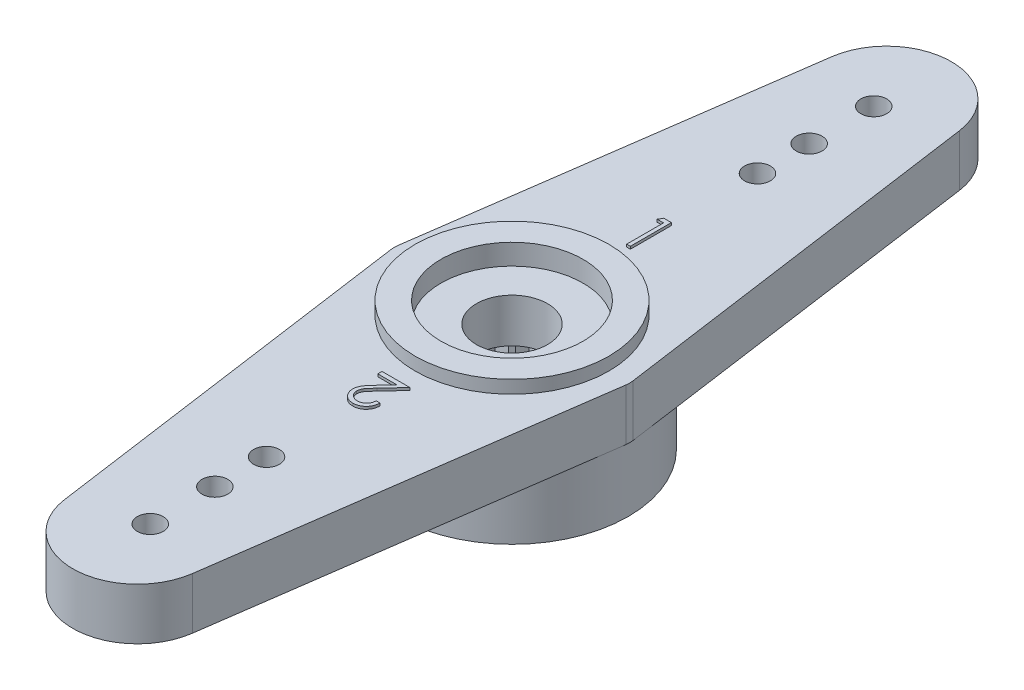
SolidWorks part; units mm, degrees
ref_plane "Front Plane" through (0, 0, 0) normal (0, 0, 1) x (1, 0, 0)
ref_plane "Top Plane" through (0, 0, 0) normal (0, 1, 0) x (1, 0, 0)
ref_plane "Right Plane" through (0, 0, 0) normal (1, 0, 0) x (0, 0, -1)
sketch "Sketch1" plane through (0, 0, 0) normal (0, 1, 0) x (1, 0, 0)
  line L0 (0, 17) -> (0, -17) construction
  line L1 (-17, 0) -> (17, 0) construction
  line L2 (-2.6883, 13.3345) -> (-4.0139, 3.9009) construction
  line L3 (4, -4) -> (-4, -4) construction
  line L4 (4, -4) -> (4, 4) construction
  line L5 (4, 4) -> (-4, 4) construction
  line L6 (-4, -4) -> (-4, 4) construction
  line L7 (4, -4) -> (-4, 4) construction
  line L8 (4, 4) -> (-4, -4) construction
  line L9 (-4, 4) -> (-2.4757, 14.8479)
  line L10 (4, 4) -> (2.4757, 14.8479)
  line L11 (4, -4) -> (2.4757, -14.8479)
  line L12 (-4, -4) -> (-2.4757, -14.8479)
  line L13 (-4, 4) -> (-4.5621, 0)
  line L14 (4, 4) -> (4.5621, 0)
  line L15 (4, -4) -> (4.5621, 0)
  line L16 (-4, -4) -> (-4.5621, 0)
  circle A0 centre (0, 0) radius 17 construction
  circle A1 centre (0, 0) radius 16 construction
  arc A2 (2.4757, 14.8479) -> (-2.4757, 14.8479) centre (0, 14.5) ccw
  arc A3 (2.4757, -14.8479) -> (-2.4757, -14.8479) centre (0, -14.5) cw
  circle A6 centre (0, 0) radius 14 construction
  circle A7 centre (0, 0) radius 11.5 construction
  circle A8 centre (0, 0) radius 9.5 construction
  circle A9 centre (0, 14) radius 0.5
  circle A10 centre (0, 11.5) radius 0.5
  circle A11 centre (0, 9.5) radius 0.5
  circle A12 centre (0, -14) radius 0.5
  circle A13 centre (0, -11.5) radius 0.5
  circle A14 centre (0, -9.5) radius 0.5
  circle A21 centre (0, 0) radius 1.375
  point P13 (-4.5621, 0)
  point P59 (0, 0)
  dimension "D1" = 34
  dimension "D2" = 1
  dimension "D3" = 5
  dimension "D5" = 8
  dimension "D6" = 8
  dimension "D7" = 2.5
  dimension "D9" = 28
  dimension "D11" = 1
  dimension "D12" = 1
  dimension "D13" = 2
  dimension "D8" = 4.5
  dimension "D10" = 1
  dimension "D14" = 2.75
extrude "Boss-Extrude1" add sketch "Sketch1" along normal blind 2
sketch "Sketch2" plane through (0, 2, 0) normal (0, 1, 0) x (1, 0, 0)
  circle A0 centre (0, 0) radius 3.75
  circle A1 centre (0, 0) radius 2.75
  dimension "D1" = 7.5
  dimension "D2" = 1
extrude "Boss-Extrude2" add sketch "Sketch2" along normal blind 0.5
sketch "Sketch3" plane through (0, 2.5, 0) normal (0, 1, 0) x (1, 0, 0)
  circle A2 centre (0, 0) radius 1.375
  circle A3 centre (0, 0) radius 2.75
  circle A5 centre (0, 0) radius 2.75
  circle A6 centre (0, 0) radius 2.75
  circle M6 centre (0, 0) radius 2.75
  dimension "D1" = 0
extrude "Cut-Extrude1" cut sketch "Sketch3" against normal blind 0.8 contours A2 M6
sketch "Sketch4" plane through (0, 0, 0) normal (0, -1, 0) x (1, 0, 0)
  circle A0 centre (0, 0) radius 4.5
  circle A1 centre (0, 0) radius 2.5
  dimension "D1" = 9
  dimension "D2" = 2
extrude "Boss-Extrude3" add sketch "Sketch4" along normal blind 2.5
sketch "Sketch5" plane through (0, -2.5, 0) normal (0, -1, 0) x (1, 0, 0)
  line L0 (0, 0) -> (0, 0.6245) construction
  line L1 (0, 3) -> (-0.299, 2.4821)
  line L2 (0, 3) -> (0.299, 2.4821)
  line L3 (0.9271, 2.8532) -> (0.4826, 2.453)
  line L4 (0.9271, 2.8532) -> (1.0514, 2.2682)
  line L5 (1.7634, 2.4271) -> (1.217, 2.1838)
  line L6 (1.7634, 2.4271) -> (1.7008, 1.8323)
  line L7 (2.4271, 1.7634) -> (1.8323, 1.7008)
  line L8 (2.4271, 1.7634) -> (2.1838, 1.217)
  line L9 (2.8532, 0.9271) -> (2.2682, 1.0514)
  line L10 (2.8532, 0.9271) -> (2.453, 0.4826)
  line L11 (3, 0) -> (2.4821, 0.299)
  line L12 (3, 0) -> (2.4821, -0.299)
  line L13 (2.8532, -0.9271) -> (2.453, -0.4826)
  line L14 (2.8532, -0.9271) -> (2.2682, -1.0514)
  line L15 (2.4271, -1.7634) -> (2.1838, -1.217)
  line L16 (2.4271, -1.7634) -> (1.8323, -1.7008)
  line L17 (1.7634, -2.4271) -> (1.7008, -1.8323)
  line L18 (1.7634, -2.4271) -> (1.217, -2.1838)
  line L19 (0.9271, -2.8532) -> (1.0514, -2.2682)
  line L20 (0.9271, -2.8532) -> (0.4826, -2.453)
  line L21 (0, -3) -> (0.299, -2.4821)
  line L22 (0, -3) -> (-0.299, -2.4821)
  line L23 (-0.9271, -2.8532) -> (-0.4826, -2.453)
  line L24 (-0.9271, -2.8532) -> (-1.0514, -2.2682)
  line L25 (-1.7634, -2.4271) -> (-1.217, -2.1838)
  line L26 (-1.7634, -2.4271) -> (-1.7008, -1.8323)
  line L27 (-2.4271, -1.7634) -> (-1.8323, -1.7008)
  line L28 (-2.4271, -1.7634) -> (-2.1838, -1.217)
  line L29 (-2.8532, -0.9271) -> (-2.2682, -1.0514)
  line L30 (-2.8532, -0.9271) -> (-2.453, -0.4826)
  line L31 (-3, 0) -> (-2.4821, -0.299)
  line L32 (-3, 0) -> (-2.4821, 0.299)
  line L33 (-2.8532, 0.9271) -> (-2.453, 0.4826)
  line L34 (-2.8532, 0.9271) -> (-2.2682, 1.0514)
  line L35 (-2.4271, 1.7634) -> (-2.1838, 1.217)
  line L36 (-2.4271, 1.7634) -> (-1.8323, 1.7008)
  line L37 (-1.7634, 2.4271) -> (-1.7008, 1.8323)
  line L38 (-1.7634, 2.4271) -> (-1.217, 2.1838)
  line L39 (-0.9271, 2.8532) -> (-1.0514, 2.2682)
  line L40 (-0.9271, 2.8532) -> (-0.4826, 2.453)
  circle A0 centre (0, 0) radius 2.5 construction
  arc A1 (-2.1838, 1.217) -> (-2.2682, 1.0514) centre (0, 0) ccw
  arc A2 (-1.7008, 1.8323) -> (-1.8323, 1.7008) centre (0, 0) ccw
  arc A3 (-1.0514, 2.2682) -> (-1.217, 2.1838) centre (0, 0) ccw
  arc A4 (-0.299, 2.4821) -> (-0.4826, 2.453) centre (0, 0) ccw
  arc A5 (0.4826, 2.453) -> (0.299, 2.4821) centre (0, 0) ccw
  arc A6 (1.217, 2.1838) -> (1.0514, 2.2682) centre (0, 0) ccw
  arc A7 (1.8323, 1.7008) -> (1.7008, 1.8323) centre (0, 0) ccw
  arc A8 (2.2682, 1.0514) -> (2.1838, 1.217) centre (0, 0) ccw
  arc A9 (2.4821, 0.299) -> (2.453, 0.4826) centre (0, 0) ccw
  arc A10 (2.453, -0.4826) -> (2.4821, -0.299) centre (0, 0) ccw
  arc A11 (2.1838, -1.217) -> (2.2682, -1.0514) centre (0, 0) ccw
  arc A12 (1.7008, -1.8323) -> (1.8323, -1.7008) centre (0, 0) ccw
  arc A13 (1.0514, -2.2682) -> (1.217, -2.1838) centre (0, 0) ccw
  arc A14 (0.299, -2.4821) -> (0.4826, -2.453) centre (0, 0) ccw
  arc A15 (-0.4826, -2.453) -> (0, -2.5) centre (0, 0) ccw
  arc A16 (-1.217, -2.1838) -> (-1.0514, -2.2682) centre (0, 0) ccw
  arc A17 (-1.8323, -1.7008) -> (-1.7008, -1.8323) centre (0, 0) ccw
  arc A18 (-2.2682, -1.0514) -> (-2.1838, -1.217) centre (0, 0) ccw
  arc A19 (-2.4821, -0.299) -> (-2.453, -0.4826) centre (0, 0) ccw
  arc A20 (-2.453, 0.4826) -> (-2.4821, 0.299) centre (0, 0) ccw
  point P68 (0, 0)
  circle M5 centre (0, 0) radius 2.5
  dimension "D1" = 30
  dimension "D2" = 3
  dimension "D3" = 20
extrude "Cut-Extrude3" cut sketch "Sketch5" against normal up to surface (2.5 mm away) contours L36 L35 M5 | L34 L33 M5 | L32 L31 M5 | L30 L29 M5 | L28 L27 M5 | L26 L25 M5 | L24 L23 M5 | L0 L21 M5 | L22 L0 M5 | L20 L19 M5 | L18 L17 M5 | L16 L15 M5 | L14 L13 M5 | L12 L11 M5 | L10 L9 M5 | L8 L7 M5 | L6 L5 M5 | L4 L3 M5 | L0 L2 M5 | L0 L1 M5 | L40 L39 M5 | L38 L37 M5
sketch "Sketch6" plane through (0, 2, 0) normal (0, 1, 0) x (1, 0, 0)
  line L1 (4.5, -4.5) -> (-4.5, -4.5) construction
  line L2 (4.5, -4.5) -> (4.5, 4.5) construction
  line L3 (4.5, 4.5) -> (-4.5, 4.5) construction
  line L4 (-4.5, -4.5) -> (-4.5, 4.5) construction
  line L5 (4.5, -4.5) -> (-4.5, 4.5) construction
  line L6 (4.5, 4.5) -> (-4.5, -4.5) construction
  circle A0 centre (0, 0) radius 4.5 construction
  text T0 "1" font "Century Gothic" height in points 6
  text T2 "2" font "Century Gothic" height in points 6
  dimension "D1" = 9
  dimension "D2" = 9
  dimension "D3" = 9
extrude "Boss-Extrude4" add sketch "Sketch6" along normal blind 0.1
fillet "Fillet1" radius 1 2 edges at (-4.5621, 1, 0) (4.5621, 1, 0)
